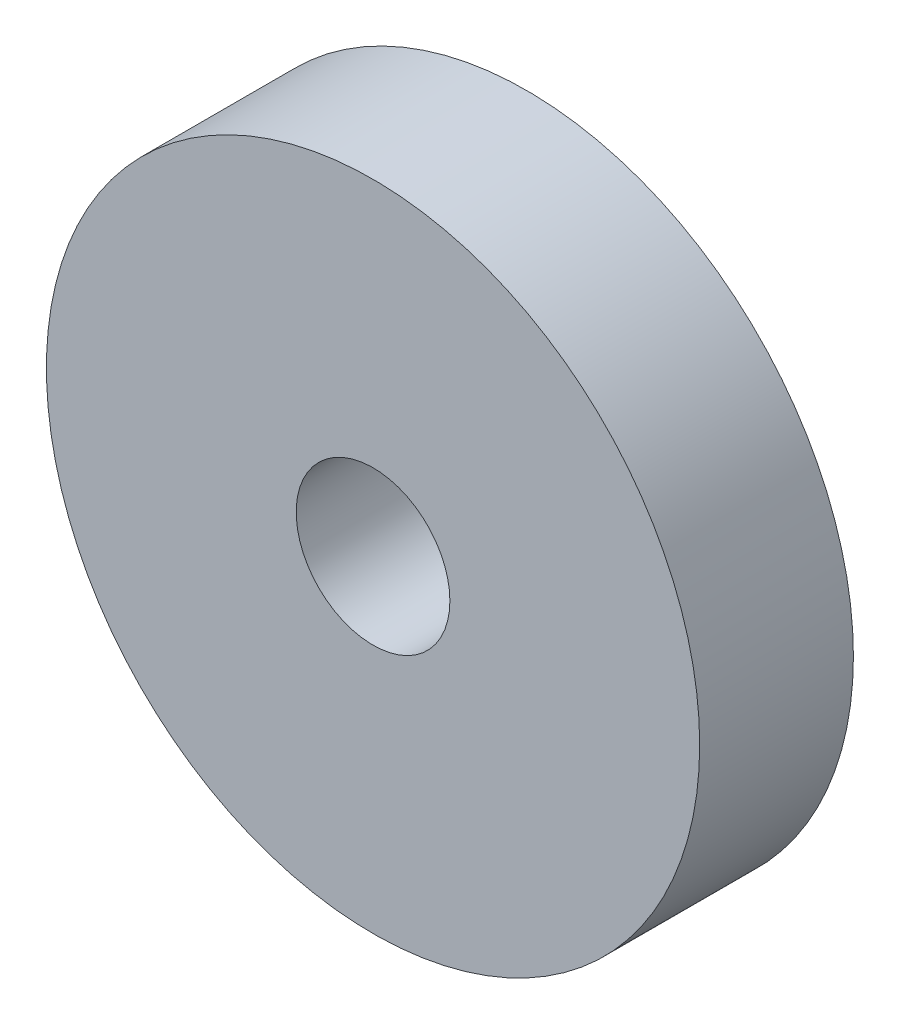
SolidWorks part; units mm, degrees
material "Rubber"
ref_plane "Front Plane" through (0, 0, 0) normal (0, 0, 1) x (1, 0, 0)
ref_plane "Top Plane" through (0, 0, 0) normal (0, 1, 0) x (1, 0, 0)
ref_plane "Right Plane" through (0, 0, 0) normal (1, 0, 0) x (0, 0, -1)
sketch "Sketch1" plane through (0, 0, 0) normal (0, 0, 1) x (1, 0, 0)
  circle A0 centre (0, 0) radius 0.5
  circle A1 centre (0, 0) radius 2.125
  dimension "D1" = 1
  dimension "D2" = 4.25
extrude "Boss-Extrude1" add sketch "Sketch1" along normal blind 1
